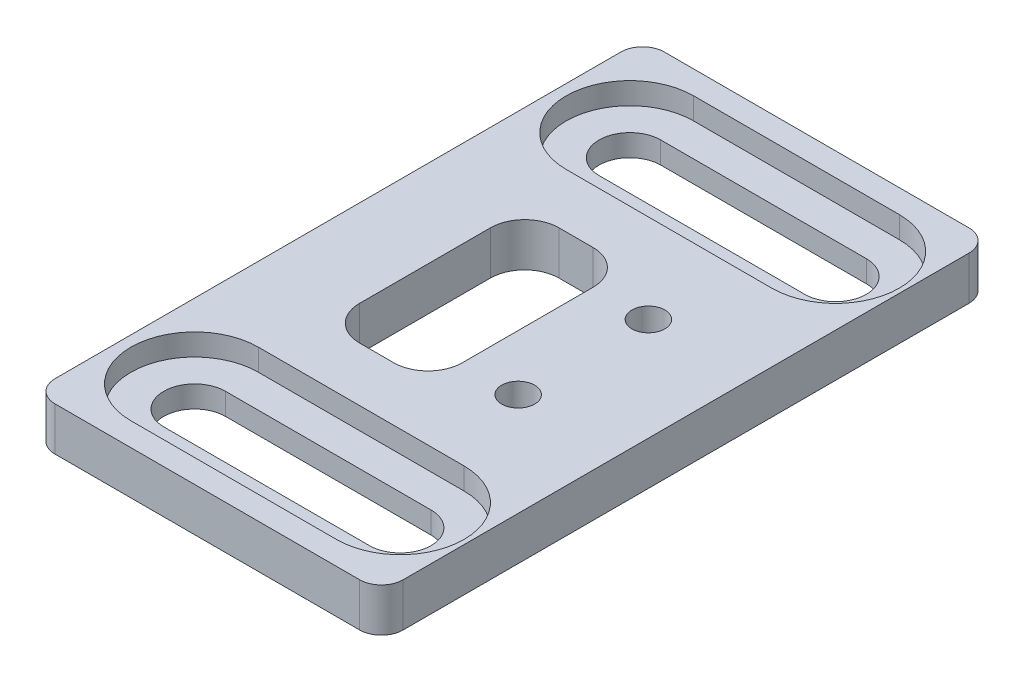
SolidWorks part; units mm, degrees
ref_plane "Front Plane" through (0, 0, 0) normal (0, 0, 1) x (1, 0, 0)
ref_plane "Top Plane" through (0, 0, 0) normal (0, 1, 0) x (1, 0, 0)
ref_plane "Right Plane" through (0, 0, 0) normal (1, 0, 0) x (0, 0, -1)
sketch "Sketch1" plane through (0, 0, 0) normal (0, 1, 0) x (1, 0, 0)
  line L0 (5.425, 6.35) -> (20.425, 6.35) construction
  line L1 (0, 0) -> (25.4, 0)
  line L2 (0, 0) -> (0, 44.45)
  line L3 (0, 44.45) -> (25.4, 44.45)
  line L4 (25.4, 0) -> (25.4, 44.45)
  line L5 (0, 0) -> (25.4, 44.45) construction
  line L6 (0, 44.45) -> (25.4, 0) construction
  line L7 (5.425, 8.6) -> (20.425, 8.6)
  line L8 (5.425, 4.1) -> (20.425, 4.1)
  line L9 (0, 22.225) -> (25.4, 22.225) construction
  line L10 (5.425, 38.1) -> (20.425, 38.1) construction
  line L11 (5.425, 35.85) -> (20.425, 35.85)
  line L12 (5.425, 40.35) -> (20.425, 40.35)
  circle A0 centre (17.9, 17.475) radius 1.2
  circle A1 centre (17.9, 26.975) radius 1.2
  arc A2 (5.425, 8.6) -> (5.425, 4.1) centre (5.425, 6.35) ccw
  arc A3 (20.425, 4.1) -> (20.425, 8.6) centre (20.425, 6.35) ccw
  arc A4 (5.425, 35.85) -> (5.425, 40.35) centre (5.425, 38.1) cw
  arc A5 (20.425, 40.35) -> (20.425, 35.85) centre (20.425, 38.1) cw
  point P4 (12.7, 22.225)
  point P10 (12.925, 6.35)
  point P21 (12.925, 38.1)
  point P26 (3.175, 38.1)
  point P35 (3.175, 6.35)
  dimension "D4" = 2.4
  dimension "D7" = 15
  dimension "D1" = 25.4
  dimension "D2" = 44.45
  dimension "D3" = 9.5
  dimension "D5" = 7.5
  dimension "D6" = 4.5
  dimension "D8" = 6.35
  dimension "D9" = 4.75
  dimension "D10" = 3.175
extrude "Boss-Extrude1" add sketch "Sketch1" along normal blind 3.175 contours L1 L4 L3 L2
sketch "Sketch2" plane through (0, 3.175, 0) normal (0, 1, 0) x (1, 0, 0)
  line L0 (5.425, 35.85) -> (20.425, 35.85) construction
  line L6 (20.425, 8.6) -> (5.425, 8.6) construction
  line L7 (11.35, 14.95) -> (8.85, 14.95)
  line L8 (13.85, 17.45) -> (13.85, 27)
  line L9 (11.35, 29.5) -> (8.85, 29.5)
  line L10 (6.35, 17.45) -> (6.35, 27)
  line L11 (13.85, 14.95) -> (6.35, 29.5) construction
  line L12 (13.85, 29.5) -> (6.35, 14.95) construction
  line L13 (0, 44.45) -> (0, 0) construction
  arc A2 (6.35, 17.45) -> (8.85, 14.95) centre (8.85, 17.45) ccw
  arc A3 (11.35, 14.95) -> (13.85, 17.45) centre (11.35, 17.45) ccw
  arc A4 (13.85, 27) -> (11.35, 29.5) centre (11.35, 27) ccw
  arc A5 (8.85, 29.5) -> (6.35, 27) centre (8.85, 27) ccw
  point P15 (10.1, 22.225)
  dimension "D5" = 2.5
  dimension "D1" = 6.35
  dimension "D2" = 6.35
  dimension "D3" = 6.35
  dimension "D4" = 7.5
extrude "Cut-Extrude1" cut sketch "Sketch2" against normal through all contours L9 A5 L10 A2 L7 A3 L8 A4
fillet "Fillet1" radius 1.5875 4 edges at (25.4, 1.5875, -44.45) (25.4, 1.5875, 0) (0, 1.5875, 0) (0, 1.5875, -44.45)
sketch "Sketch3" plane through (0, 3.175, 0) normal (0, 1, 0) x (1, 0, 0)
  line L39 (5.425, 33.45) -> (20.425, 33.45)
  line L40 (20.425, 42.75) -> (5.425, 42.75)
  line L41 (5.425, 33.45) -> (20.425, 33.45)
  line L42 (20.425, 42.75) -> (5.425, 42.75)
  line L49 (5.425, 1.7) -> (20.425, 1.7)
  line L50 (20.425, 11) -> (5.425, 11)
  line L51 (5.425, 1.7) -> (20.425, 1.7)
  line L52 (20.425, 11) -> (5.425, 11)
  arc A30 (20.425, 33.45) -> (20.425, 42.75) centre (20.425, 38.1) ccw
  arc A31 (5.425, 42.75) -> (5.425, 33.45) centre (5.425, 38.1) ccw
  arc A32 (20.425, 33.45) -> (20.425, 42.75) centre (20.425, 38.1) ccw
  arc A33 (5.425, 42.75) -> (5.425, 33.45) centre (5.425, 38.1) ccw
  arc A38 (20.425, 1.7) -> (20.425, 11) centre (20.425, 6.35) ccw
  arc A39 (5.425, 11) -> (5.425, 1.7) centre (5.425, 6.35) ccw
  arc A40 (20.425, 1.7) -> (20.425, 11) centre (20.425, 6.35) ccw
  arc A41 (5.425, 11) -> (5.425, 1.7) centre (5.425, 6.35) ccw
  dimension "D1" = 2.4
  dimension "D2" = 2.4
extrude "Cut-Extrude2" cut sketch "Sketch3" against normal blind 1.5875 contours L41 A32 L42 A33
ref_plane "Plane1" through (0, 0, 0) normal (0, -1, 0) x (-1, 0, 0)
